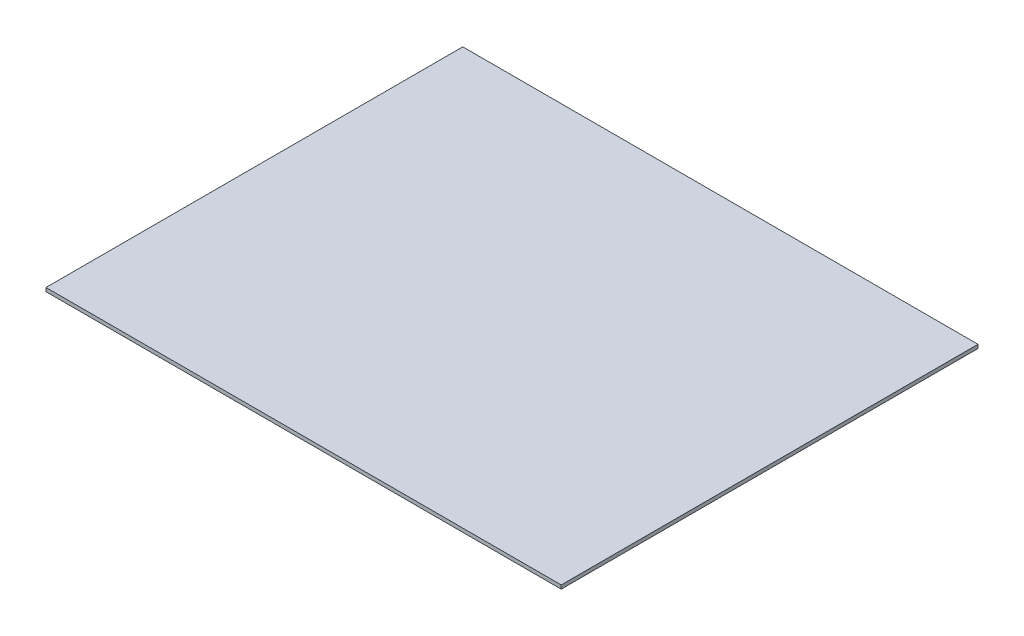
SolidWorks part; units mm, degrees
ref_plane "Front Plane" through (0, 0, 0) normal (0, 0, 1) x (1, 0, 0)
ref_plane "Top Plane" through (0, 0, 0) normal (0, 1, 0) x (1, 0, 0)
ref_plane "Right Plane" through (0, 0, 0) normal (1, 0, 0) x (0, 0, -1)
sketch "Sketch1" plane through (0, 0, 0) normal (0, 1, 0) x (1, 0, 0)
  line L1 (123, 99.5) -> (-123, 99.5)
  line L2 (123, 99.5) -> (123, -99.5)
  line L3 (123, -99.5) -> (-123, -99.5)
  line L4 (-123, 99.5) -> (-123, -99.5)
  line L5 (123, 99.5) -> (-123, -99.5) construction
  line L6 (123, -99.5) -> (-123, 99.5) construction
  point P0 (0, 0)
  dimension "D1" = 246
  dimension "D2" = 199
extrude "Boss-Extrude1" add sketch "Sketch1" along normal blind 1.75
